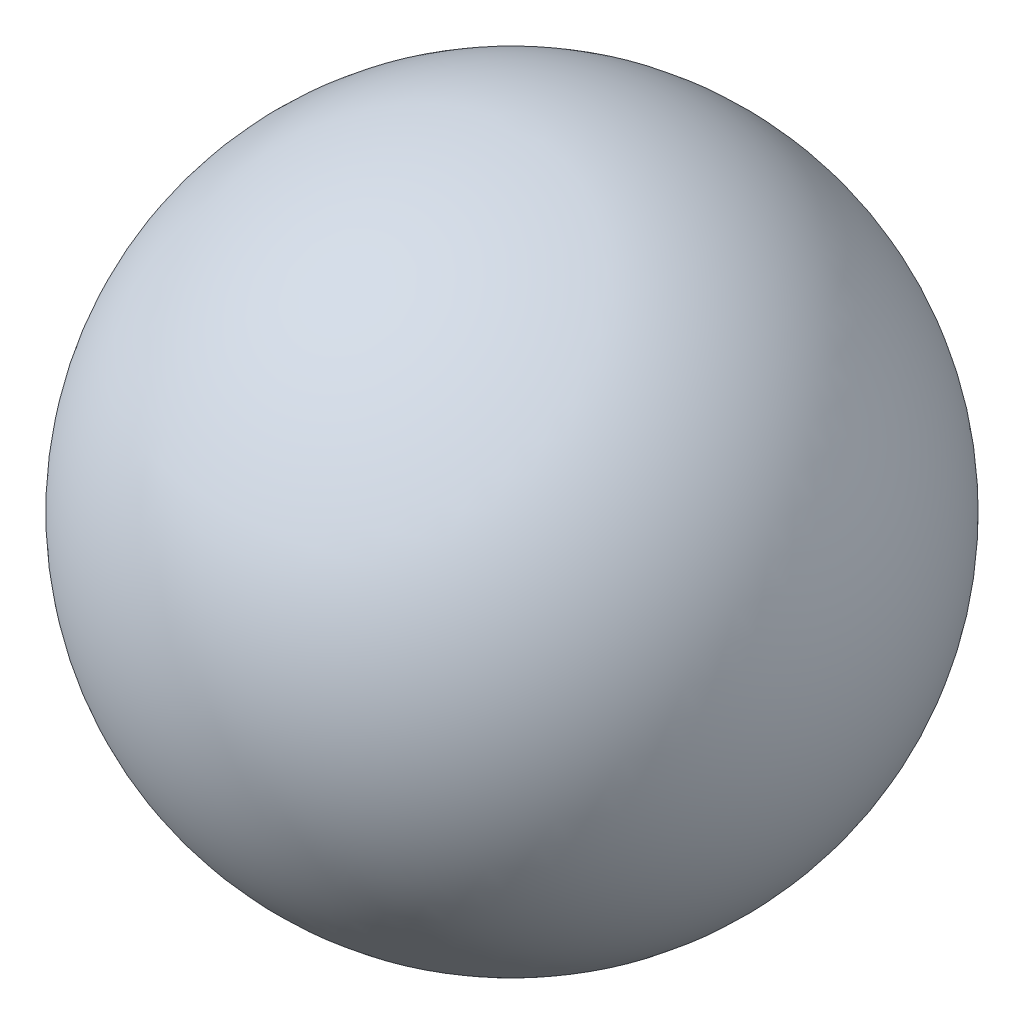
SolidWorks part; units mm, degrees
material "Chrome Stainless Steel"
ref_plane "Front" through (0, 0, 0) normal (0, 0, 1) x (1, 0, 0)
ref_plane "Top" through (0, 0, 0) normal (0, 1, 0) x (1, 0, 0)
ref_plane "Right" through (0, 0, 0) normal (1, 0, 0) x (0, 0, -1)
sketch "Sketch1" plane through (0, 0, 0) normal (0, 0, 1) x (1, 0, 0)
  line L0 (0, 0) -> (0, 12.7)
  arc A0 (0, 12.7) -> (0, 0) centre (0, 6.35) cw
  dimension "D1" = 12.7
revolve "Revolve1" add sketch "Sketch1" angle 360 about L0
